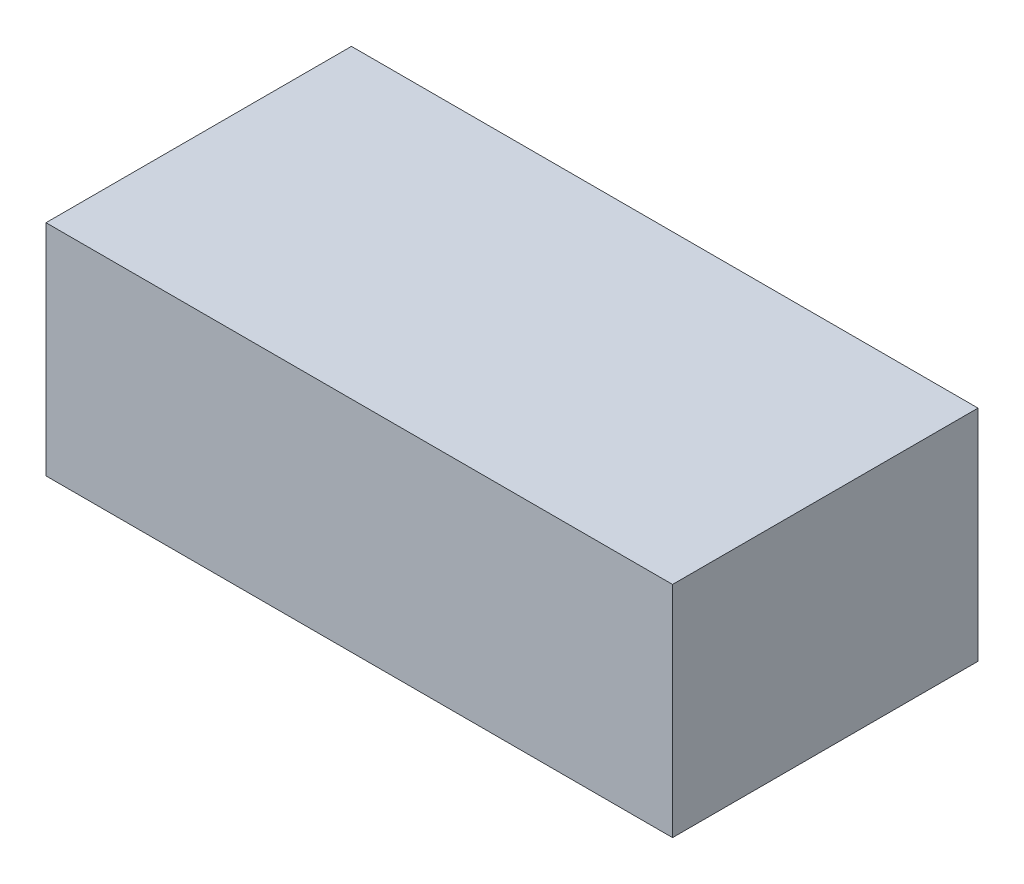
SolidWorks part; units mm, degrees
ref_plane "Front Plane" through (0, 0, 0) normal (0, 0, 1) x (1, 0, 0)
ref_plane "Top Plane" through (0, 0, 0) normal (0, 1, 0) x (1, 0, 0)
ref_plane "Right Plane" through (0, 0, 0) normal (1, 0, 0) x (0, 0, -1)
sketch "Sketch1" plane through (0, 0, 0) normal (0, 1, 0) x (1, 0, 0)
  line L1 (0, 0) -> (80, 0)
  line L2 (0, 0) -> (0, 39)
  line L3 (0, 39) -> (80, 39)
  line L4 (80, 0) -> (80, 39)
  dimension "D1" = 80
  dimension "D2" = 39
extrude "Boss-Extrude1" add sketch "Sketch1" along normal blind 28
